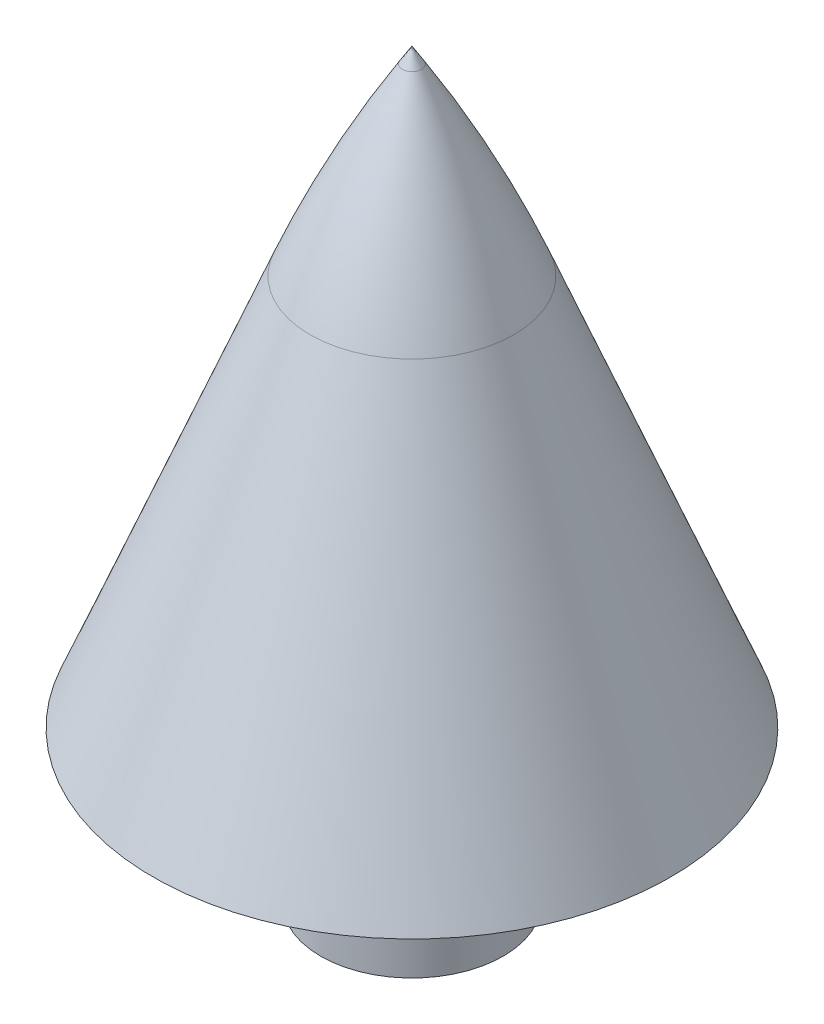
SolidWorks part; units mm, degrees
material "1060 Alloy"
ref_plane "Front Plane" through (0, 0, 0) normal (0, 0, 1) x (1, 0, 0)
ref_plane "Top Plane" through (0, 0, 0) normal (0, 1, 0) x (1, 0, 0)
ref_plane "Right Plane" through (0, 0, 0) normal (1, 0, 0) x (0, 0, -1)
sketch "Sketch1" plane through (0, 0, 0) normal (0, 1, 0) x (1, 0, 0)
  circle A0 centre (0, 0) radius 3
  circle A1 centre (0, 0) radius 1.585
  dimension "D1" = 6
  dimension "D2" = 3.17
extrude "Boss-Extrude1" add sketch "Sketch1" along normal blind 5
sketch "Sketch4" plane through (0, 0, 0) normal (0, 0, 1) x (1, 0, 0)
  line L0 (0, 0) -> (0, 22.4104) construction
  line L1 (0, 0) -> (5.9759, 0) construction
  line L2 (-8.5, 5) -> (0, 5) construction
  line L3 (8.5, 5) -> (2.085, 21)
  line L4 (-8.5, 5) -> (-2.085, 21) construction
  line L5 (-2.085, 21) -> (2.085, 21) construction
  line L6 (8.5, 5) -> (8.5, 21) construction
  line L7 (8.5, 21) -> (2.085, 21) construction
  line L8 (1.585, 5) -> (-1.585, 5) construction
  line L9 (0, 5) -> (8.5, 5)
  line L10 (2.085, 21) -> (0, 21)
  line L11 (0, 5) -> (0, 21)
  point P7 (0, 21)
  dimension "D2" = 0
  dimension "D1" = 17
  dimension "D4" = 4.17
  dimension "D5" = 16
revolve "Revolve6" add sketch "Sketch4" angle 360 about L11
sketch "Sketch7" plane through (0, 0, 0) normal (0, 0, 1) x (1, 0, 0)
  line L0 (0, 21) -> (0, 25.118) construction
  line L1 (2.085, 21) -> (-2.085, 21) construction
  line L2 (0, 21) -> (2.085, 21)
  line L3 (2.085, 21) -> (0, 24.3982)
  line L4 (0, 21) -> (0, 24.3982)
revolve "Revolve7" add sketch "Sketch7" angle 360 about L4
fillet "Fillet1" radius 40 1 edges at (0, 21, -2.085)
sketch "Sketch8" plane through (0, 5, 0) normal (0, -1, 0) x (1, 0, 0)
  circle A0 centre (0, 0) radius 1.585
extrude "Cut-Extrude1" cut sketch "Sketch8" against normal blind 7
